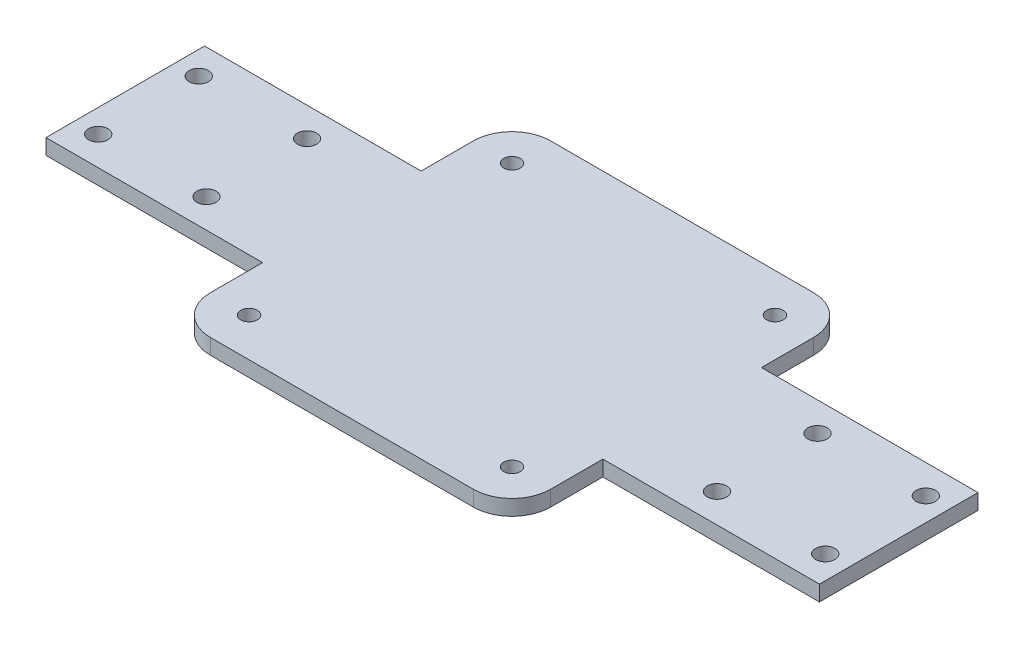
SolidWorks part; units mm, degrees
ref_plane "Front Plane" through (0, 0, 0) normal (0, 0, 1) x (1, 0, 0)
ref_plane "Top Plane" through (0, 0, 0) normal (0, 1, 0) x (1, 0, 0)
ref_plane "Right Plane" through (0, 0, 0) normal (1, 0, 0) x (0, 0, -1)
sketch "Sketch1" plane through (0, 0, 0) normal (0, 1, 0) x (1, 0, 0)
  line L1 (44, -44) -> (-44, -44)
  line L2 (44, -44) -> (44, 44)
  line L3 (44, 44) -> (-44, 44)
  line L4 (-44, -44) -> (-44, 44)
  line L5 (44, -44) -> (-44, 44) construction
  line L6 (44, 44) -> (-44, -44) construction
  point P0 (0, 0)
  dimension "D1" = 88
extrude "Boss-Extrude1" add sketch "Sketch1" along normal blind 4
fillet "Fillet1" radius 10 4 edges at (-44, 2, 44) (44, 2, 44) (44, 2, -44) (-44, 2, -44)
sketch "Sketch2" plane through (0, 4, 0) normal (0, 1, 0) x (1, 0, 0)
  circle A0 centre (34, 34) radius 2.15
  circle A1 centre (-34, 34) radius 2.15
  circle A2 centre (34, -34) radius 2.15
  circle A3 centre (-34, -34) radius 2.15
  dimension "D1" = 4.3
extrude "Cut-Extrude1" cut sketch "Sketch2" against normal through all
sketch "Sketch3" plane through (0, 0, 0) normal (0, 1, 0) x (1, 0, 0)
  line L1 (100, -20.5) -> (-100, -20.5)
  line L2 (100, -20.5) -> (100, 20.5)
  line L3 (100, 20.5) -> (-100, 20.5)
  line L4 (-100, -20.5) -> (-100, 20.5)
  line L5 (100, -20.5) -> (-100, 20.5) construction
  line L6 (100, 20.5) -> (-100, -20.5) construction
  point P0 (0, 0)
  dimension "D1" = 200
  dimension "D2" = 41
extrude "Boss-Extrude2" add sketch "Sketch3" along normal up to surface (4 mm away) up to face at (-34, 4, -31.85)
sketch "Sketch5" plane through (0, 0, 0) normal (0, -1, 0) x (1, 0, 0)
  line L0 (-100, -20.5) -> (-100, 20.5) construction
  line L1 (-66, -13) -> (-94, -13) construction
  line L2 (-66, -13) -> (-66, 13) construction
  line L3 (-66, 13) -> (-94, 13) construction
  line L4 (-94, -13) -> (-94, 13) construction
  line L5 (-66, -13) -> (-94, 13) construction
  line L6 (-66, 13) -> (-94, -13) construction
  circle A0 centre (-66, 13) radius 2.5
  circle A1 centre (-66, -13) radius 2.5
  circle A2 centre (-94, -13) radius 2.5
  circle A3 centre (-94, 13) radius 2.5
  point P0 (-80, 0)
  dimension "D4" = 5
  dimension "D1" = 28
  dimension "D2" = 26
  dimension "D3" = 6
extrude "Cut-Extrude2" cut sketch "Sketch5" against normal through all
mirror "Mirror1" about plane through (0, 0, 0) normal (1, 0, 0) of "Cut-Extrude2"
